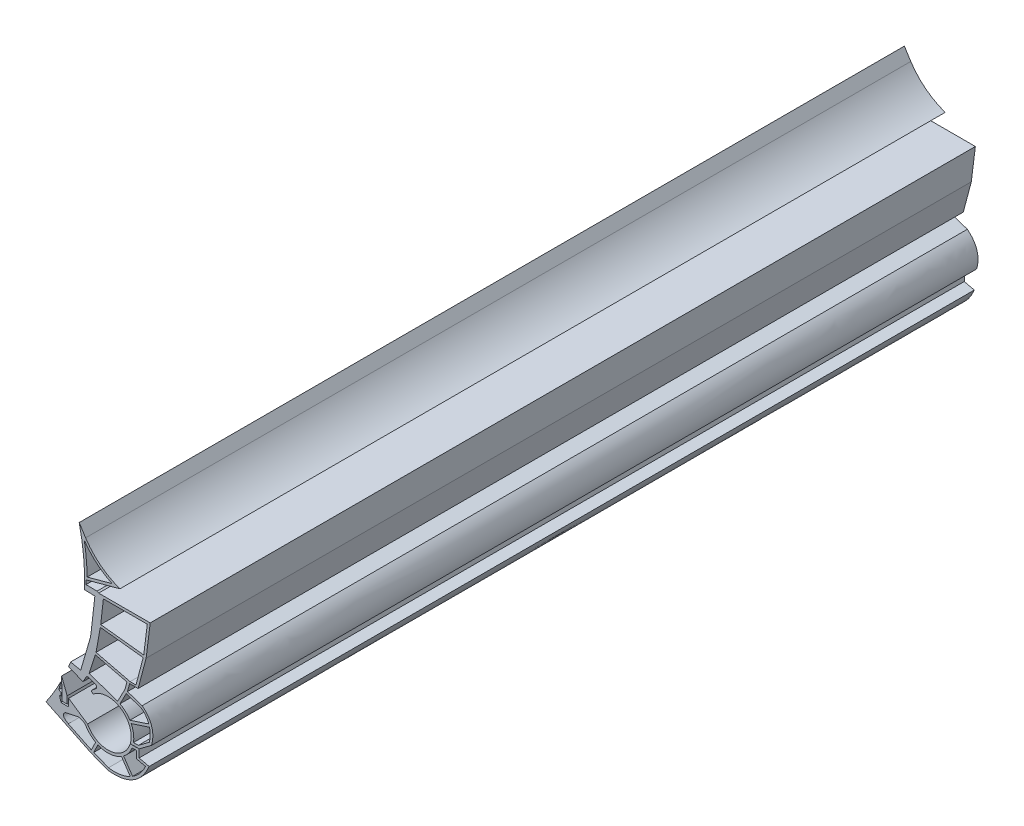
SolidWorks part; units mm, degrees
ref_plane "Front Plane" through (0, 0, 0) normal (0, 0, 1) x (1, 0, 0)
ref_plane "Top Plane" through (0, 0, 0) normal (0, 1, 0) x (1, 0, 0)
ref_plane "Right Plane" through (0, 0, 0) normal (1, 0, 0) x (0, 0, -1)
sketch "Sketch2" plane through (0, 0, 0) normal (0, 0, 1) x (1, 0, 0)
  line L0 (219.8777, -7.3333) -> (209.8833, -7)
  line L1 (0, 0) -> (-263.0213, 0) construction
  line L2 (0, 0) -> (503.4039, -495.904) construction
  line L3 (211.27, 2) -> (211.27, -2.0122)
  line L4 (211.27, 2) -> (244.2248, 10.9559)
  line L5 (172.5123, -119.7477) -> (0, 0) construction
  line L15 (219.8777, -7.3333) -> (216.2013, -40.0243)
  line L18 (216.2013, -40.0243) -> (215.3965, -44.7697)
  line L19 (215.3965, -44.7697) -> (206.1632, -76.4518)
  line L20 (206.1632, -76.4518) -> (196.3725, -74.4167)
  line L21 (211.27, -2.0122) -> (221.9905, -2.1143)
  line L22 (221.9905, -2.1143) -> (223.531, -3.0278)
  line L23 (223.531, -3.0278) -> (273.531, -3.0278)
  line L24 (273.531, -3.0278) -> (269.5848, -34.6396)
  line L25 (270.6995, -5.5278) -> (267.2551, -33.1197)
  line L26 (269.5848, -34.6396) -> (261.8286, -63.9775)
  line L27 (221.0289, -54.0081) -> (254.0572, -62.0786)
  line L28 (0, 0) -> (249.8676, 117.227) construction
  line L29 (194.4329, -79.3464) -> (208.321, -85.014)
  line L30 (208.321, -85.014) -> (211.4883, -79.5598)
  line L31 (213.9226, -78.6925) -> (220.3562, -81.1152)
  line L32 (220.9321, -84.523) -> (216.9052, -87.8804)
  line L33 (216.9874, -89.4782) -> (218.3705, -90.4086)
  line L35 (259.7447, -62.0786) -> (254.0572, -62.0786)
  line L36 (253.5706, -63.9204) -> (251.5029, -71.7468)
  line L37 (250.3263, -73.992) -> (244.2248, -85.6346)
  line L38 (0, 0) -> (206.8337, 36.3293) construction
  line L39 (216.4695, -141.0372) -> (172.5123, -119.7477)
  line L40 (0, 0) -> (266.1101, 73.2218) construction
  line L41 (262.0645, -111.5732) -> (272.6191, -103.753)
  line L42 (0, 0) -> (266.2927, -262.3254)
  line L43 (262.8897, -114.0732) -> (274.807, -105.2433)
  line L44 (272.1073, -88.5776) -> (253.8581, -94.589)
  line L45 (262.7547, -114.2735) -> (262.7547, -121.8261)
  line L46 (262.7547, -121.8261) -> (272.5005, -124.0668)
  line L47 (256.4413, -140.3984) -> (247.7441, -127.6847)
  line L49 (216.4695, -141.0372) -> (232.5974, -147.2083)
  line L50 (218.7349, -139.2273) -> (233.1976, -144.7612)
  line L51 (250.3263, -73.992) -> (264.5337, -78.6507)
  line L58 (0, 0) -> (187.6646, -90.5081) construction
  line L59 (210.9083, 37.045) -> (271.8386, 47.7471) construction
  line L60 (188.0432, -111.5043) -> (187.6612, -90.5031)
  line L61 (187.6612, -90.5031) -> (193.0432, -104.5043)
  line L62 (193.0432, -104.5043) -> (193.0432, -111.5043)
  line L63 (193.0432, -111.5043) -> (188.0432, -111.5043)
  line L64 (186.9304, -95.6923) -> (184.9361, -103.4416)
  line L65 (184.9361, -103.4416) -> (187.2928, -104.5043)
  line L66 (187.2928, -104.5043) -> (187.2928, -107.5043)
  line L67 (187.2928, -107.5043) -> (185.6123, -108.0133)
  line L68 (185.6123, -108.0133) -> (187.1661, -113.1431)
  line L69 (187.1661, -113.1431) -> (194.4851, -113.1431)
  line L70 (194.4851, -113.1431) -> (194.4851, -105.8318)
  line L71 (194.4851, -105.8318) -> (212.7725, -118.3053)
  line L72 (194.116, -127.4331) -> (216.4688, -138.2591)
  line L73 (220.6116, -129.7051) -> (216.4688, -138.2591)
  line L74 (222.8262, -130.7798) -> (218.7349, -139.2273)
  line L75 (255.9459, -116.7734) -> (260.2547, -116.7734)
  line L76 (217.3629, -138.7023) -> (233.4908, -144.8734) construction
  line L77 (217.6412, -141.4855) -> (217.5945, -141.582)
  line L78 (254.2667, -141.6473) -> (245.6804, -129.0956)
  line L79 (210.9083, 37.045) -> (204.7084, 46.8453)
  line L80 (254.187, -114.0735) -> (262.8897, -114.0732)
  line L81 (257.3305, -111.5734) -> (262.0645, -111.5732)
  line L82 (254.1276, -114.2735) -> (262.7547, -114.2735)
  line L84 (272.8896, -90.9524) -> (255.0889, -96.8163)
  line L85 (261.4014, -112.0645) -> (273.3187, -103.2346) construction
  line L86 (212.4433, 4.9095) -> (236.5064, 11.449)
  line L87 (249.1578, -70.8359) -> (241.9523, -84.5852)
  line L88 (249.2885, -70.5864) -> (242.0104, -84.4742) construction
  line L89 (210.6144, 4.4125) -> (243.5692, 13.3684) construction
  line L91 (220.2694, -56.3961) -> (250.9895, -63.9025)
  line L92 (228.1312, -5.5278) -> (270.6995, -5.5278)
  line L93 (228.1312, -5.5278) -> (225.5556, -28.4301)
  line L94 (223.531, -5.5278) -> (273.531, -5.5278) construction
  line L95 (225.1937, -30.9051) -> (221.0289, -54.0081)
  line L96 (220.2694, -56.3961) -> (214.3288, -75.0738)
  line L99 (267.2551, -33.1197) -> (225.5556, -28.4301)
  line L101 (241.9523, -84.5852) -> (214.3288, -75.0738)
  line L102 (213.2576, -52.1092) -> (261.8286, -63.9775) construction
  line L103 (212.6641, -54.5378) -> (261.2352, -66.406) construction
  line L104 (261.8286, -63.9775) -> (253.5706, -63.9204)
  line L105 (250.9895, -63.9025) -> (249.1578, -70.8359)
  line L110 (266.7506, -35.5787) -> (225.1937, -30.9051)
  line L111 (260.2547, -116.7734) -> (260.2547, -123.8165)
  line L112 (260.2547, -123.8165) -> (268.949, -125.8154)
  line L113 (266.7506, -35.5787) -> (259.7447, -62.0786)
  line L116 (262.1946, -124.2625) -> (271.9403, -126.5032) construction
  line L117 (260.2547, -114.2735) -> (260.2547, -121.8261) construction
  line L118 (262.7547, -116.7734) -> (262.7548, -116.7734)
  line L119 (251.5029, -71.7468) -> (244.2248, -85.6346) construction
  line L120 (251.5029, -71.7468) -> (265.7561, -76.4206)
  arc A2 (212.7725, -118.3053) -> (254.1276, -114.2735) centre (232.6203, -107.7781) ccw
  arc A3 (210.781, -119.9456) -> (220.6116, -129.7051) centre (232.6203, -107.7781) ccw
  arc A4 (247.7441, -127.6847) -> (255.9459, -116.7734) centre (232.6203, -107.7781) ccw
  arc A5 (222.8262, -130.7798) -> (245.6804, -129.0956) centre (232.6203, -107.7781) ccw
  arc A6 (257.3305, -111.5734) -> (255.0889, -96.8163) centre (232.6203, -107.7781) ccw
  arc A7 (254.187, -114.0735) -> (218.3705, -90.4086) centre (232.6203, -107.7781) ccw
  arc A8 (253.8581, -94.589) -> (244.2248, -85.6346) centre (232.6203, -107.7781) ccw
  arc A9 (272.1073, -88.5776) -> (264.5337, -78.6507) centre (254.3312, -94.2872) ccw
  arc A10 (272.6191, -103.753) -> (272.8896, -90.9524) centre (247.5808, -96.8206) ccw
  arc A11 (220.3562, -81.1152) -> (220.9321, -84.523) centre (219.6514, -82.9869) cw
  arc A12 (216.9874, -89.4782) -> (216.9052, -87.8804) centre (217.5456, -88.6485) cw
  arc A13 (211.4883, -79.5598) -> (213.9226, -78.6925) centre (213.2178, -80.5642) cw
  arc A14 (233.1976, -144.7612) -> (254.2667, -141.6473) centre (239.2703, -113.0158) ccw
  arc A15 (256.4413, -140.3984) -> (268.949, -125.8154) centre (239.2703, -113.0158) ccw
  arc A20 (196.3725, -74.4167) -> (194.4329, -79.3464) centre (0, 0) cw
  arc A21 (194.4329, -79.3464) -> (196.3725, -74.4167) centre (0, 0) ccw
  arc A25 (244.2248, 10.9559) -> (210.9083, 37.045) centre (266.1101, 73.2218) cw
  arc A26 (212.4433, 4.9095) -> (209.7046, 34.3544) centre (0, 0) ccw
  arc A27 (209.8833, -7) -> (204.7084, 46.8453) centre (0, 0) ccw
  arc A28 (236.5064, 11.449) -> (209.7046, 34.3544) centre (266.1101, 73.2218) cw
  arc A30 (186.9304, -95.6923) -> (172.5123, -119.7477) centre (0, 0) cw
  spline S1 degree 2 poles (265.7561, -76.4206) (279.7328, -87.7185) (274.807, -105.2433) knots 0 0 0 1 1 1
  spline S2 degree 2 poles (272.5005, -124.0668) (261.1875, -150.6063) (232.5974, -147.2083) knots 0 0 0 1 1 1
  spline S3 degree 2 poles (203.5127, -116.7914) (197.6982, -118.0086) (191.8838, -119.2259) knots 0.316119 0.316119 0.316119 1 1 1
  spline S4 degree 2 poles (191.8838, -119.2259) (185.6555, -122.2651) (194.116, -127.4331) knots 0 0 0 1 1 1
  spline S5 degree 2 poles (203.5127, -116.7914) (207.7583, -116.9752) (210.781, -119.9456) knots 0 0 0 1 1 1
  point P54 (186.9304, -95.6923)
  point P94 (149.6027, -147.3738)
  dimension "D3" = 59.9
  dimension "D10" = 8
  dimension "D23" = 1
  dimension "D6" = 2.5
  dimension "D4" = 2.5
  dimension "D9" = 15
  dimension "D11" = 2.5
  dimension "D12" = 2.5
  dimension "D13" = 2.5
  dimension "D14" = 2.5
  dimension "D15" = 2.5
  dimension "D17" = 2.5
extrude "Boss-Extrude1" add sketch "Sketch2" along normal blind 800
